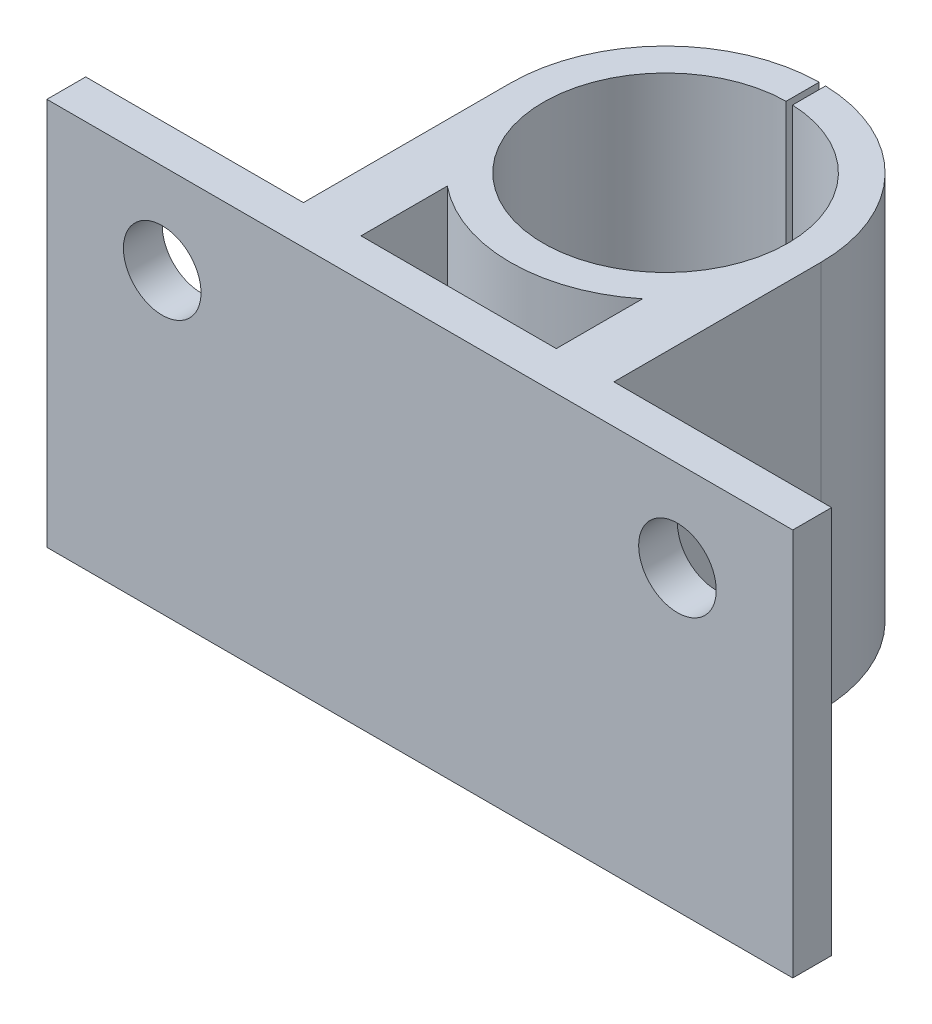
SolidWorks part; units mm, degrees
ref_plane "Front Plane" through (0, 0, 0) normal (0, 0, 1) x (1, 0, 0)
ref_plane "Top Plane" through (0, 0, 0) normal (0, 1, 0) x (1, 0, 0)
ref_plane "Right Plane" through (0, 0, 0) normal (1, 0, 0) x (0, 0, -1)
sketch "Sketch1" plane through (0, 0, 0) normal (0, 1, 0) x (1, 0, 0)
  line L1 (-28.8339, 15) -> (28.8339, 15)
  line L2 (-28.8339, 15) -> (-28.8339, -15)
  line L3 (-28.8339, -15) -> (28.8339, -15)
  line L4 (28.8339, 15) -> (28.8339, -15)
  line L5 (-28.8339, 15) -> (28.8339, -15) construction
  line L6 (-28.8339, -15) -> (28.8339, 15) construction
  point P0 (0, 0)
  dimension "D1" = 30
extrude "Boss-Extrude1" add sketch "Sketch1" along normal blind 30
sketch "Sketch2" plane through (0, 30, 0) normal (0, 1, 0) x (1, 0, 0)
  circle A0 centre (0, 4) radius 4
  dimension "D1" = 8
extrude "Cut-Extrude2" cut sketch "Sketch2" against normal blind 40
sketch "Sketch4" plane through (0, 30, 0) normal (0, 1, 0) x (1, 0, 0)
  line L0 (11, 4) -> (11, -12)
  line L1 (11, -12) -> (28.8339, -12)
  line L2 (28.8339, -15) -> (28.8339, 15) construction
  line L3 (28.8339, -12) -> (28.8339, -15)
  line L4 (28.8339, -15) -> (-28.8339, -15)
  line L5 (-28.8339, -15) -> (-28.8339, -12)
  line L6 (-28.8339, 15) -> (-28.8339, -15) construction
  line L7 (-28.8339, -12) -> (-11, -12)
  line L8 (-11, -12) -> (-11, 4)
  line L9 (-28.8339, -12) -> (-28.8339, 15)
  line L10 (-28.8339, 15) -> (28.8339, 15)
  line L11 (28.8339, 15) -> (28.8339, -12)
  line L12 (-7.5498, -4) -> (-7.5498, -12)
  line L13 (-7.5498, -12) -> (7.5498, -12)
  line L14 (7.5498, -12) -> (7.5498, -4)
  circle A0 centre (0, 4) radius 11
  circle A1 centre (0, 4) radius 8
  line M6 (28.8339, -15) -> (28.8339, 15)
  line M7 (28.8339, 15) -> (-28.8339, 15)
  line M8 (-28.8339, 15) -> (-28.8339, -15)
  circle M23 centre (0, 4) radius 4
  dimension "D5" = 22
  dimension "D6" = 16
  dimension "D1" = 3
  dimension "D2" = 3
  dimension "D3" = 8
  dimension "D4" = 8
extrude "Cut-Extrude3" cut sketch "Sketch4" against normal through all contours A1 M23 | A0 L10 L7 L8 M8 | A0 L0 L1 M6 M7 | A0 L12 L13 L14
sketch "Sketch5" plane through (0, 0, 12) normal (0, 0, -1) x (-1, 0, 0)
  line L0 (28.8339, 30) -> (11, 30) construction
  line L1 (-11, 30) -> (-28.8339, 30) construction
  circle A0 centre (-19.917, 23) radius 3
  circle A1 centre (19.917, 23) radius 3
  dimension "D3" = 6
  dimension "D4" = 6
  dimension "D1" = 7
  dimension "D2" = 7
extrude "Cut-Extrude4" cut sketch "Sketch5" against normal through all
sketch "Sketch6" plane through (0, 30, 0) normal (0, 1, 0) x (1, 0, 0)
  circle A0 centre (0, 4) radius 9.45
  dimension "D1" = 18.9
extrude "Cut-Extrude6" cut sketch "Sketch6" against normal through all
sketch "Sketch7" plane through (0, 30, 0) normal (0, 1, 0) x (1, 0, 0)
  line L0 (12.0019, 4) -> (12.0019, -12)
  line L1 (11, -12) -> (28.8339, -12) construction
  line L2 (12.0019, -12) -> (7.5498, -12)
  line L3 (7.5498, -12) -> (7.5498, -5.3299)
  line L4 (7.5498, -12) -> (7.5498, -4) construction
  line L5 (-12.0019, 4) -> (-12.0019, -12)
  line L6 (-28.8339, -12) -> (-11, -12) construction
  line L7 (-12.0019, -12) -> (-7.5498, -12)
  line L8 (-7.5498, -12) -> (-7.5498, -5.3299)
  line L9 (-7.5498, -4) -> (-7.5498, -12) construction
  circle A0 centre (0, 4) radius 12.0019
  circle A1 centre (0, 4) radius 9.45
  circle A2 centre (0, 4) radius 11
  line M3 (-7.5498, -12) -> (-7.5498, -4)
  line M5 (7.5498, -4) -> (7.5498, -12)
  line M7 (11, -12) -> (11, 4)
  arc M8 (11, 4) -> (-11, 4) centre (0, 4) ccw
  line M9 (-11, 4) -> (-11, -12)
  line M10 (-11, -12) -> (-28.8339, -12)
  line M14 (28.8339, -12) -> (11, -12)
extrude "Boss-Extrude2" add sketch "Sketch7" against normal through all contours A0 L2 M5 M7 | A0 L0 M7 M14 | A0 L7 M9 M3 | A0 L5 M10 M9 | A0 M7 M9 M8 | A1
sketch "Sketch8" plane through (0, 30, 0) normal (0, 1, 0) x (1, 0, 0)
  line L1 (0.372, 12.0019) -> (-0.128, 12.0019)
  line L2 (0.372, 12.0019) -> (0.372, 18.2018)
  line L3 (0.372, 18.2018) -> (-0.128, 18.2018)
  line L4 (-0.128, 12.0019) -> (-0.128, 18.2018)
  dimension "D1" = 0.5
extrude "Cut-Extrude7" cut sketch "Sketch8" against normal through all
